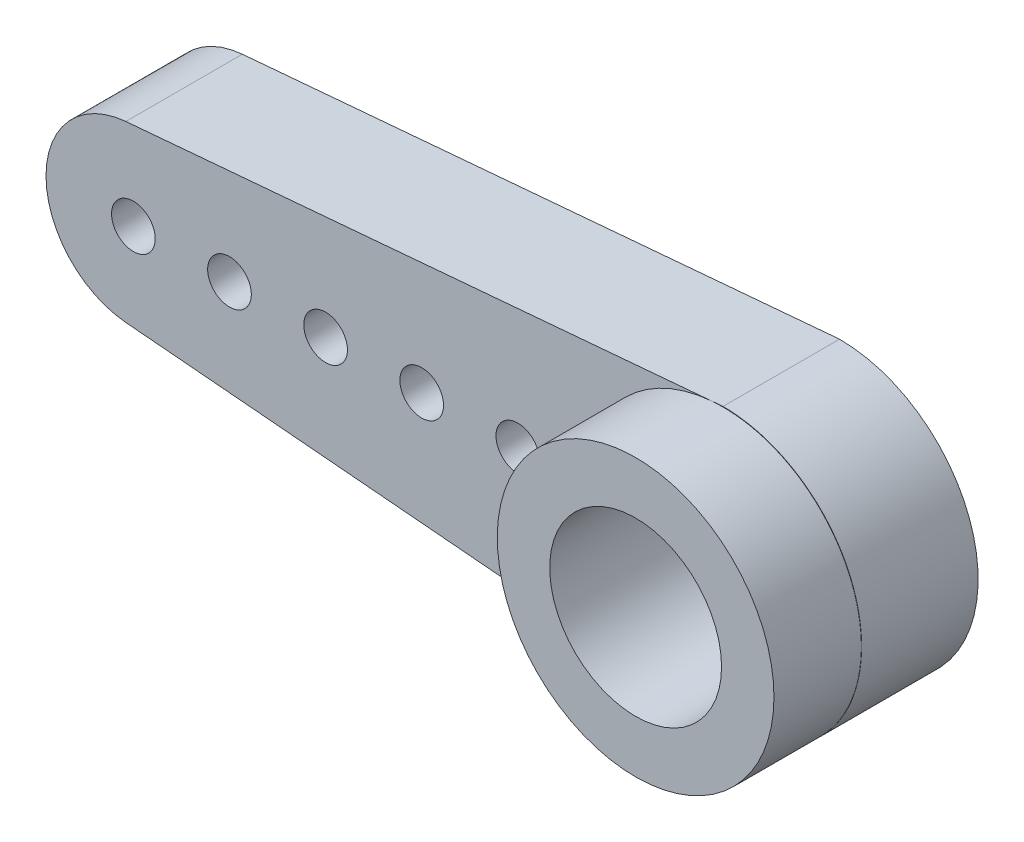
SolidWorks part; units mm, degrees
material "1060 Alloy"
ref_plane "Front Plane" through (0, 0, 0) normal (0, 0, 1) x (1, 0, 0)
ref_plane "Top Plane" through (0, 0, 0) normal (0, 1, 0) x (1, 0, 0)
ref_plane "Right Plane" through (0, 0, 0) normal (1, 0, 0) x (0, 0, -1)
sketch "Sketch1" plane through (0, 0, 0) normal (0, 0, 1) x (1, 0, 0)
  line L0 (0, 4.7678) -> (-20.5041, 2.9888)
  line L1 (-20.2447, 0) -> (0, 0) construction
  line L2 (-20.5041, -2.9888) -> (-0.4106, -4.7322)
  line L3 (-20.2447, 0) -> (-16.9447, 0) construction
  circle A0 centre (0, 0) radius 2.95
  circle A1 centre (0, 0) radius 4.75 construction
  circle A2 centre (-20.2447, 0) radius 3 construction
  arc A3 (-20.5041, 2.9888) -> (-20.5041, -2.9888) centre (-20.2447, 0) ccw
  arc A4 (0, 4.7678) -> (-0.4106, -4.7322) centre (0.0008, 0.0089) cw
  circle A8 centre (-20.2447, 0) radius 0.75
  circle A9 centre (-16.9447, 0) radius 0.75
  circle A10 centre (-13.6447, 0) radius 0.75
  circle A11 centre (-10.3447, 0) radius 0.75
  circle A12 centre (-7.0447, 0) radius 0.75
  point P11 (-23.2447, 0)
  point P13 (4.7553, -0.1966)
  dimension "D1" = 9.5
  dimension "D2" = 3
  dimension "D3" = 28
  dimension "D4" = 5.9
  dimension "D5" = 1.5
  dimension "D7" = 3.3
  dimension "D6" = 5
extrude "Boss-Extrude1" add sketch "Sketch1" along normal blind 4
sketch "Sketch2" plane through (0, 0, 4) normal (0, 0, 1) x (1, 0, 0)
  circle A0 centre (0, 0) radius 4.75
  circle A1 centre (0, 0) radius 2.95
  circle A2 centre (0, 0) radius 2.95 construction
  arc A3 (-0.4106, -4.7322) -> (0, 4.7678) centre (0.0008, 0.0089) ccw construction
extrude "Boss-Extrude2" add sketch "Sketch2" along normal blind 3
move or copy body "Body-Move/Copy1" [suppressed] bodies to move or copy 102 parameters "D1"=0, "D2"=0, "D3"=0
